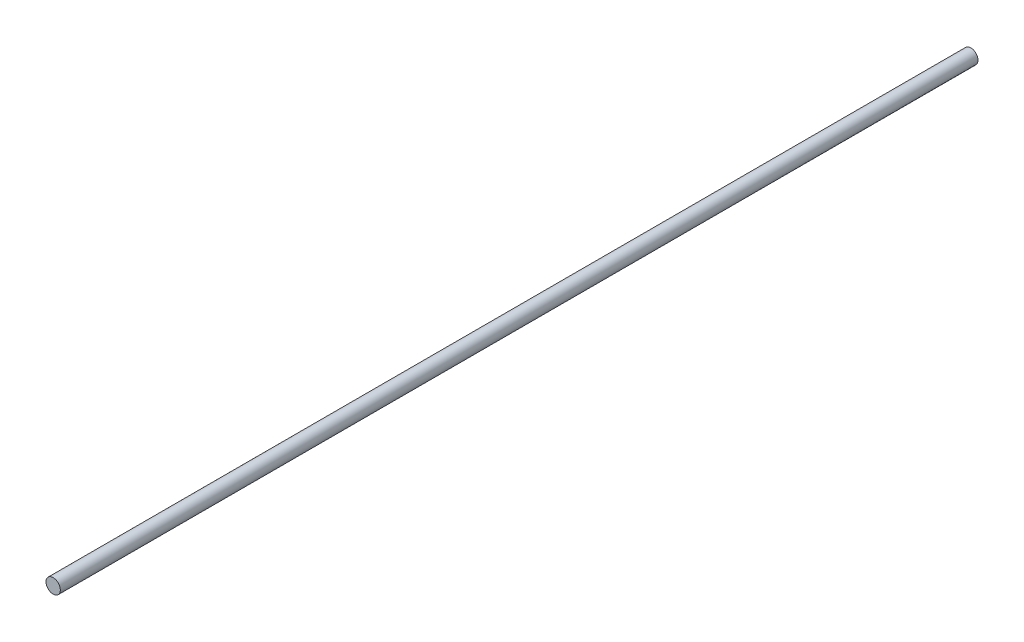
SolidWorks part; units mm, degrees
ref_plane "Front Plane" through (0, 0, 0) normal (0, 0, 1) x (1, 0, 0)
ref_plane "Top Plane" through (0, 0, 0) normal (0, 1, 0) x (1, 0, 0)
ref_plane "Right Plane" through (0, 0, 0) normal (1, 0, 0) x (0, 0, -1)
sketch "Sketch1" plane through (0, 0, 0) normal (0, 0, 1) x (1, 0, 0)
  circle A0 centre (0, 0) radius 4
extrude "Boss-Extrude1" add sketch "Sketch1" along normal blind 512
